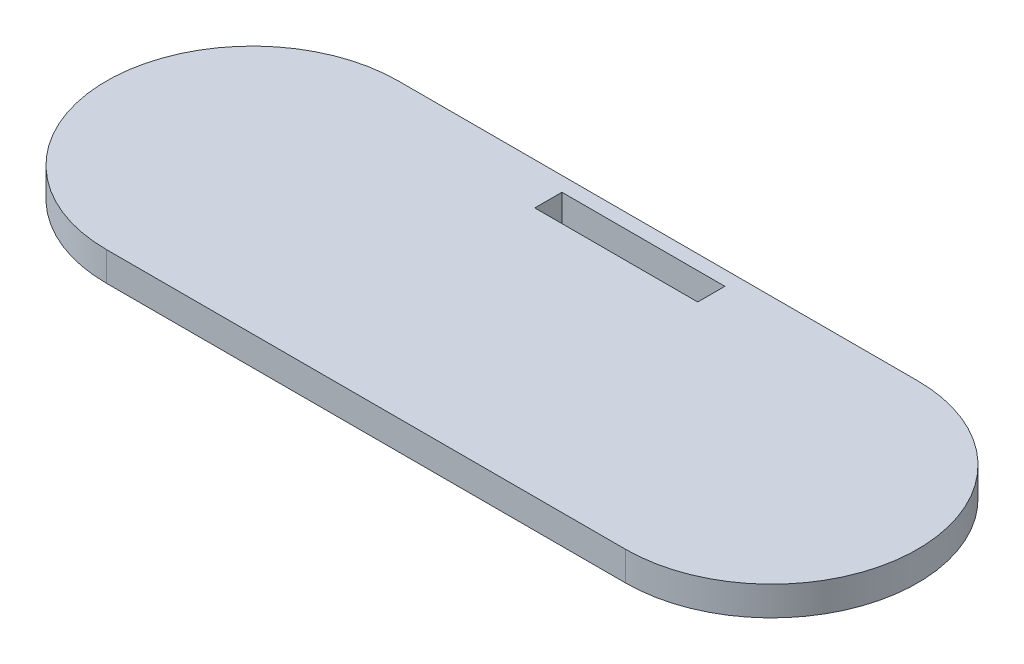
SolidWorks part; units mm, degrees
ref_plane "Front Plane" through (0, 0, 0) normal (0, 0, 1) x (1, 0, 0)
ref_plane "Top Plane" through (0, 0, 0) normal (0, 1, 0) x (1, 0, 0)
ref_plane "Right Plane" through (0, 0, 0) normal (1, 0, 0) x (0, 0, -1)
sketch "Sketch1" plane through (0, 0, 0) normal (0, 1, 0) x (1, 0, 0)
  line L0 (0, 0) -> (177.8, 0) construction
  line L1 (0, 50) -> (177.8, 50)
  line L2 (0, -50) -> (177.8, -50)
  line L4 (61, 45) -> (116.8, 45)
  line L5 (61, 45) -> (61, 35.7)
  line L6 (61, 35.7) -> (116.8, 35.7)
  line L7 (116.8, 45) -> (116.8, 35.7)
  arc A0 (0, 50) -> (0, -50) centre (0, 0) ccw
  arc A1 (177.8, -50) -> (177.8, 50) centre (177.8, 0) ccw
  point P3 (88.9, 0)
  point P12 (88.9, 35.7)
  dimension "D2" = 50
  dimension "D6" = 277.8
  dimension "D1" = 177.8
  dimension "D3" = 55.8
  dimension "D4" = 9.3
  dimension "D5" = 5
extrude "Boss-Extrude1" add sketch "Sketch1" along normal blind 10
